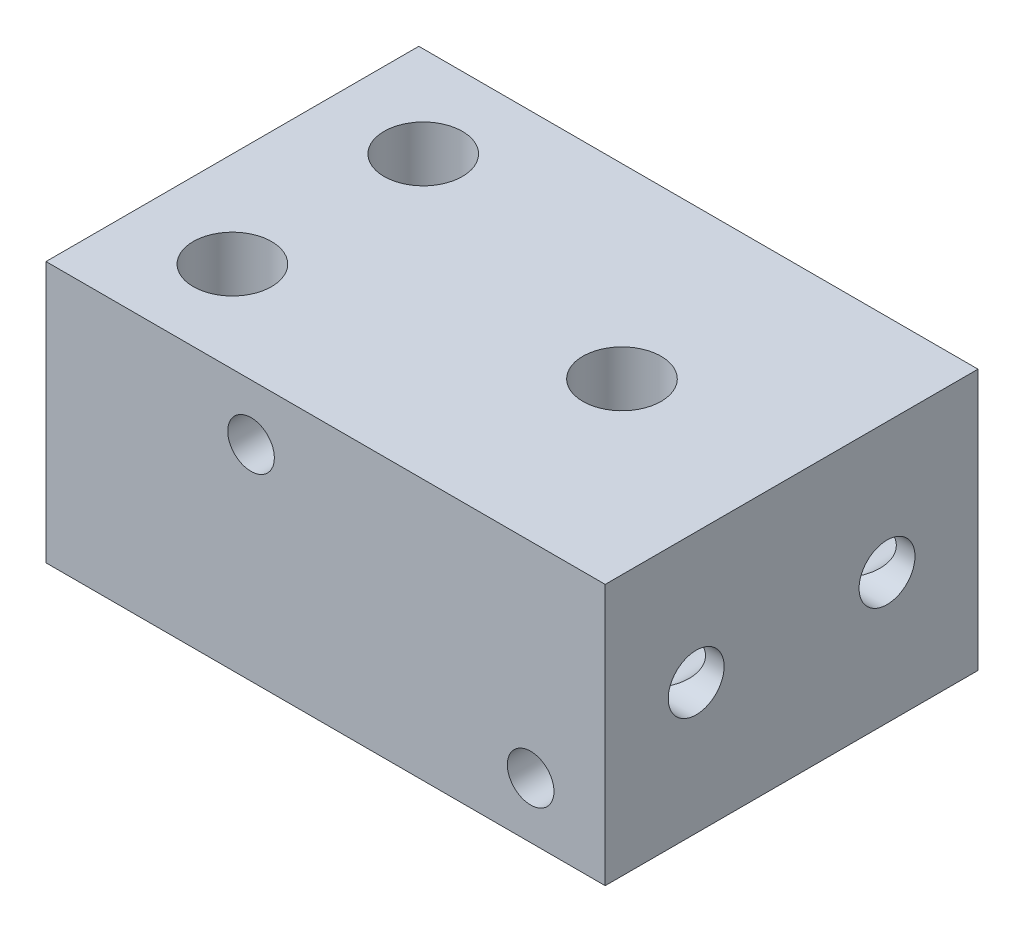
SolidWorks part; units mm, degrees
ref_plane "Front Plane" through (0, 0, 0) normal (0, 0, 1) x (1, 0, 0)
ref_plane "Top Plane" through (0, 0, 0) normal (0, 1, 0) x (1, 0, 0)
ref_plane "Right Plane" through (0, 0, 0) normal (1, 0, 0) x (0, 0, -1)
sketch "Sketch1" plane through (0, 0, 0) normal (0, 0, 1) x (1, 0, 0)
  line L1 (-15, -7) -> (15, -7)
  line L2 (-15, -7) -> (-15, 7)
  line L3 (-15, 7) -> (15, 7)
  line L4 (15, -7) -> (15, 7)
  line L5 (-15, -7) -> (15, 7) construction
  line L6 (-15, 7) -> (15, -7) construction
  point P0 (0, 0)
  dimension "D1" = 30
  dimension "D2" = 14
extrude "Boss-Extrude1" add sketch "Sketch1" along normal mid plane 20
sketch "Sketch2" plane through (0, 0, 10) normal (0, 0, 1) x (1, 0, 0)
  line L1 (15, -7) -> (15, 7) construction
  circle A0 centre (11.5, 0) radius 1.5
  point P5 (11.5, 0)
  dimension "D1" = 2
  dimension "D2" = 3
sketch "Sketch3" plane through (0, 7, 0) normal (0, 1, 0) x (1, 0, 0)
  circle A0 centre (5.9, 0) radius 2.5 construction
  circle A1 centre (5.9, 0) radius 1
  dimension "D1" = 5
  dimension "D2" = 2
extrude "Cut-Extrude2" cut sketch "Sketch3" against normal through all
hole_wizard "M5 Tapped Hole1" positions "Sketch5" profile "Sketch4" tap size "M5" standard "ISO"
sketch "Sketch5" plane through (0, 7, 0) normal (0, 1, 0) x (1, 0, 0)
  point P0 (5.9, 0)
sketch "Sketch4" plane through (5.9, 7, 0) normal (1, 0, 0) x (0, 0, 1)
  line L0 (0, 0) -> (0, 9.2618)
  line L1 (0, 9.2618) -> (2.1, 8)
  line L2 (2.1, 8) -> (2.1, 0)
  line L5 (2.1, 0) -> (0, 0)
  line L10 (0, 9.2618) -> (-2.1, 8) construction
  line L11 (0, -6.35) -> (0, 107.95) construction
  dimension "Tap Drill Dia." = 4.2
  dimension "Tap Drill Depth" = 8
  dimension "Drill Angle" = 118
cosmetic thread "Hole Thread1" parameters "D1"=5, "D2"=5
sketch "Sketch6" plane through (0, 7, 0) normal (0, 1, 0) x (1, 0, 0)
  line L0 (5.9, 0) -> (-16.8004, 0) construction
  line L1 (-15, -10) -> (-15, 10) construction
  line L2 (-5.8812, 7.4282) -> (-9.8812, 9.7376) construction
  line L3 (-9.8812, 9.7376) -> (-13.8812, 7.4282) construction
  line L4 (-13.8812, 7.4282) -> (-13.8812, 2.8094) construction
  line L5 (-13.8812, 2.8094) -> (-9.8812, 0.5) construction
  line L6 (-9.8812, 0.5) -> (-5.8812, 2.8094) construction
  line L7 (-5.8812, 2.8094) -> (-5.8812, 7.4282) construction
  line L8 (-7.5718, 9.1188) -> (-12.1906, 9.1188) construction
  line L9 (-12.1906, 9.1188) -> (-14.5, 5.1188) construction
  line L10 (-14.5, 5.1188) -> (-12.1906, 1.1188) construction
  line L11 (-12.1906, 1.1188) -> (-7.5718, 1.1188) construction
  line L12 (-7.5718, 1.1188) -> (-5.2624, 5.1188) construction
  line L13 (-5.2624, 5.1188) -> (-7.5718, 9.1188) construction
  circle A0 centre (-9.8812, 5.1188) radius 4 construction
  circle A1 centre (-9.8812, 5.1188) radius 4 construction
  point P22 (-9.8812, 5.1188)
  dimension "D1" = 8
  dimension "D2" = 0.5
  dimension "D3" = 8
  dimension "D4" = 0.5
hole_wizard "M5 Tapped Hole2" positions "Sketch8" profile "Sketch7" tap size "M5" standard "ISO"
sketch "Sketch8" plane through (0, 7, 0) normal (0, 1, 0) x (1, 0, 0)
  point P0 (-9.8812, 5.1188)
sketch "Sketch7" plane through (-9.8812, 7, -5.1188) normal (1, 0, 0) x (0, 0, 1)
  line L0 (0, 0) -> (0, 11.2618)
  line L1 (0, 11.2618) -> (2.1, 10)
  line L2 (2.1, 10) -> (2.1, 0)
  line L5 (2.1, 0) -> (0, 0)
  line L10 (0, 11.2618) -> (-2.1, 10) construction
  line L11 (0, -6.35) -> (0, 107.95) construction
  dimension "Tap Drill Dia." = 4.2
  dimension "Tap Drill Depth" = 10
  dimension "Drill Angle" = 118
cosmetic thread "Hole Thread2" parameters "D1"=5, "D2"=5
mirror "Mirror1" about plane through (0, 0, 0) normal (0, 0, 1) of "M5 Tapped Hole2"
sketch "Sketch17" plane through (0, 0, -10) normal (0, 0, -1) x (-1, 0, 0)
  line L0 (-15, -7) -> (-15, 7) construction
  circle A0 centre (-12.5, 0) radius 1.5 construction
  point P6 (-12.5, 0)
  dimension "D1" = 3
  dimension "D2" = 1
hole_wizard "Ø3.0 (3) Diameter Hole4" positions "Sketch19" profile "Sketch18" hole size "Ø3.0" standard "ISO"
sketch "Sketch19" plane through (0, 0, -10) normal (0, 0, -1) x (-1, 0, 0)
  point P0 (-12.5, 0)
sketch "Sketch18" plane through (12.5, 0, -10) normal (1, 0, 0) x (0, 1, 0)
  line L0 (0, 0) -> (0, 15.9013)
  line L1 (0, 15.9013) -> (1.5, 15)
  line L2 (1.5, 15) -> (1.5, 0)
  line L5 (1.5, 0) -> (0, 0)
  line L10 (0, 15.9013) -> (-1.5, 15) construction
  line L11 (0, -6.35) -> (0, 107.95) construction
  dimension "Hole Dia." = 3
  dimension "Hole Depth" = 15
  dimension "Drill Angle" = 118
sketch "Sketch20" plane through (15, 0, 0) normal (1, 0, 0) x (0, 0, -1)
  line L0 (-5.9013, 0) -> (10, 0) construction
  line L1 (-5.1188, -4.2618) -> (-5.1188, 7) construction
  line L2 (-5.1188, -3) -> (-5.1188, 7) construction
  line L3 (-5.1188, -3) -> (-5.1188, -4.2618) construction
  line L4 (5.1188, -4.2618) -> (5.1188, 7) construction
  point P15 (-5.1188, 0)
  point P16 (5.1188, 0)
hole_wizard "Ø3.0 (3) Diameter Hole5" positions "Sketch22" profile "Sketch21" hole size "Ø3.0" standard "ISO"
sketch "Sketch22" plane through (15, 0, 0) normal (1, 0, 0) x (0, 0, -1)
  point P0 (-5.1188, 0)
  point P3 (5.1188, 0)
sketch "Sketch21" plane through (15, 0, 5.1188) normal (0, 1, 0) x (0, 0, -1)
  line L0 (0, 0) -> (0, 25.9013)
  line L1 (0, 25.9013) -> (1.5, 25)
  line L2 (1.5, 25) -> (1.5, 0)
  line L5 (1.5, 0) -> (0, 0)
  line L10 (0, 25.9013) -> (-1.5, 25) construction
  line L11 (0, -6.35) -> (0, 107.95) construction
  dimension "Hole Dia." = 3
  dimension "Hole Depth" = 25
  dimension "Drill Angle" = 118
hole_wizard "M3 Tapped Hole1" positions "Sketch25" profile "Sketch24" tap size "M3" standard "ISO"
sketch "Sketch25" plane through (0, 0, 10) normal (0, 0, 1) x (1, 0, 0)
  line L0 (-8.4115, 0) -> (12.5, 0) construction
  point P0 (-4, 4)
  point P2 (11, -4)
  dimension "D1" = 4
  dimension "D2" = 4
  dimension "D3" = 11
  dimension "D4" = 4
sketch "Sketch24" plane through (-4, 4, 10) normal (1, 0, 0) x (0, -1, 0)
  line L0 (0, 0) -> (0, 8.2511)
  line L1 (0, 8.2511) -> (1.25, 7.5)
  line L2 (1.25, 7.5) -> (1.25, 0)
  line L5 (1.25, 0) -> (0, 0)
  line L10 (0, 8.2511) -> (-1.25, 7.5) construction
  line L11 (0, -6.35) -> (0, 107.95) construction
  dimension "Tap Drill Dia." = 2.5
  dimension "Tap Drill Depth" = 7.5
  dimension "Drill Angle" = 118
cosmetic thread "Hole Thread4" parameters "D1"=5, "D2"=3
cosmetic thread "Hole Thread5" parameters "D1"=5, "D2"=3
